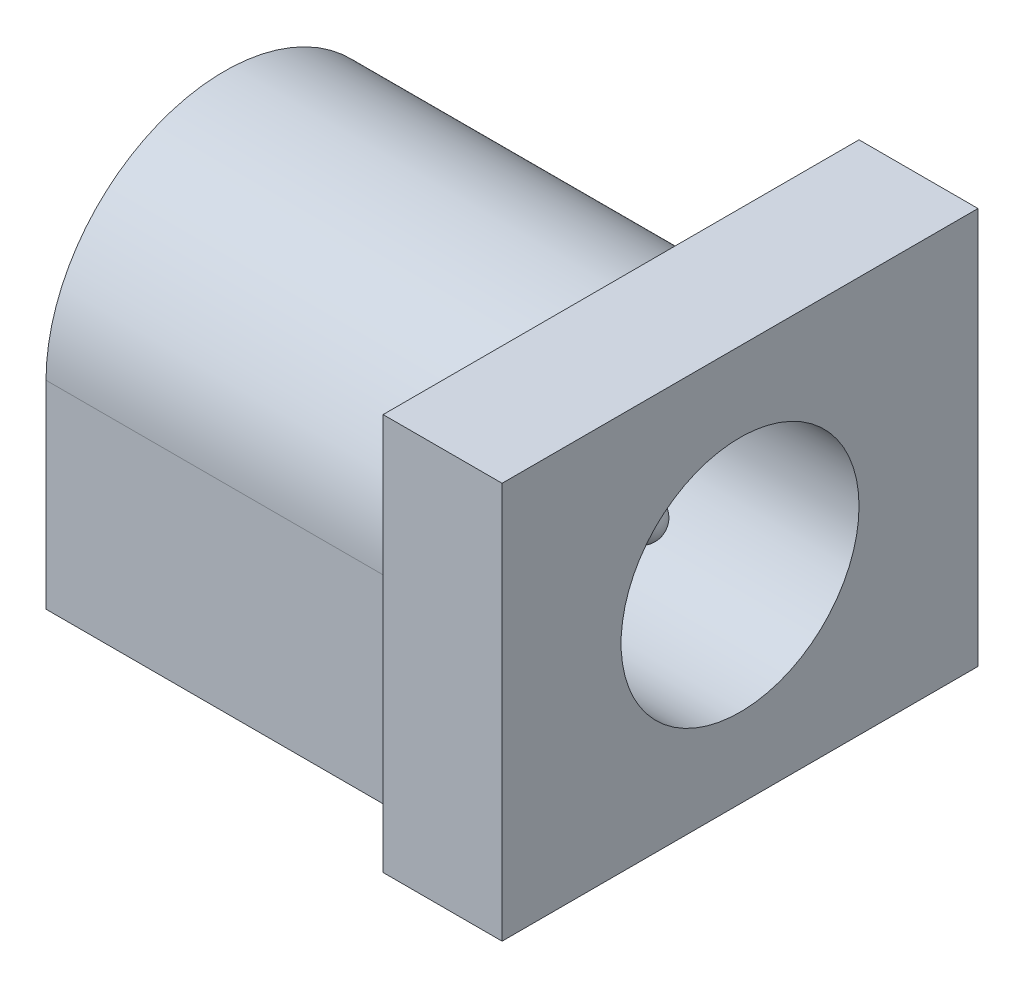
SolidWorks part; units mm, degrees
ref_plane "Front Plane" through (0, 0, 0) normal (0, 0, 1) x (1, 0, 0)
ref_plane "Top Plane" through (0, 0, 0) normal (0, 1, 0) x (1, 0, 0)
ref_plane "Right Plane" through (0, 0, 0) normal (1, 0, 0) x (0, 0, -1)
sketch "Sketch1" plane through (0, 0, 0) normal (1, 0, 0) x (0, 0, -1)
  line L0 (0, 0) -> (0, 14.4457) construction
  line L1 (-4.5, 0) -> (4.5, 0)
  line L2 (-4.5, 0) -> (-4.5, 5)
  line L4 (4.5, 0) -> (4.5, 5)
  arc A0 (-4.5, 5) -> (4.5, 5) centre (0, 5) cw
  dimension "D1" = 9
  dimension "D2" = 5
extrude "Boss-Extrude1" add sketch "Sketch1" along normal blind 10
sketch "Sketch2" plane through (10, 0, 0) normal (1, 0, 0) x (0, 0, -1)
  line L0 (0, 0) -> (0, 13.744) construction
  line L1 (-6, 0) -> (6, 0)
  line L2 (-6, 0) -> (-6, 10)
  line L3 (-6, 10) -> (6, 10)
  line L4 (6, 0) -> (6, 10)
  dimension "D1" = 12
  dimension "D2" = 10
extrude "Boss-Extrude2" add sketch "Sketch2" along normal blind 3
sketch "Sketch3" plane through (13, 0, 0) normal (1, 0, 0) x (0, 0, -1)
  circle A0 centre (0, 5) radius 3
  dimension "D1" = 6
extrude "Cut-Extrude1" cut sketch "Sketch3" against normal blind 12
sketch "Sketch4" plane through (1, 0, 0) normal (1, 0, 0) x (0, 0, -1)
  circle A0 centre (0, 5) radius 0.5
  dimension "D1" = 1
extrude "Boss-Extrude3" add sketch "Sketch4" along normal blind 10
fillet "Fillet1" radius 0.5 1 edges at (11, 5, -0.5)
